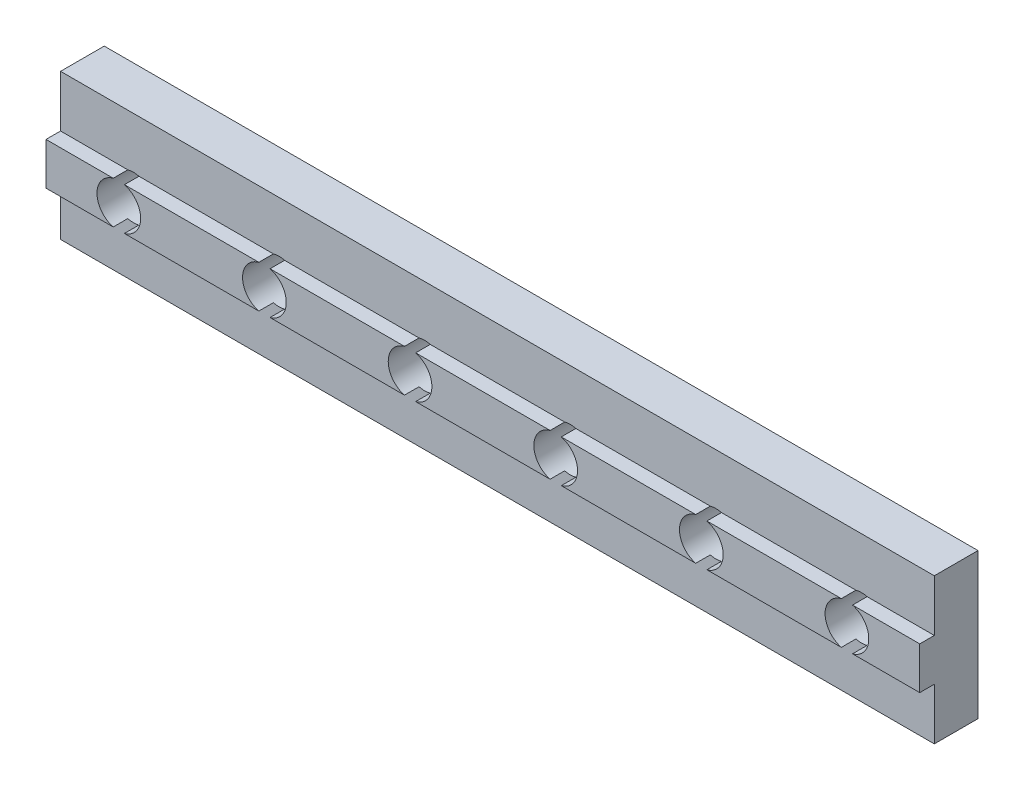
SolidWorks part; units mm, degrees
ref_plane "Front Plane" through (0, 0, 0) normal (0, 0, 1) x (1, 0, 0)
ref_plane "Top Plane" through (0, 0, 0) normal (0, 1, 0) x (1, 0, 0)
ref_plane "Right Plane" through (0, 0, 0) normal (1, 0, 0) x (0, 0, -1)
sketch "Esquisse1" plane through (0, 0, 0) normal (0, 0, 1) x (1, 0, 0)
  line L1 (0, 0) -> (60, 0)
  line L2 (0, 0) -> (0, 10)
  line L3 (0, 10) -> (60, 10)
  line L4 (60, 0) -> (60, 10)
  dimension "D1" = 60
  dimension "D2" = 10
extrude "Boss.-Extru.1" add sketch "Esquisse1" along normal blind 3
sketch "Esquisse2" plane through (0, 0, 3) normal (0, 0, 1) x (1, 0, 0)
  line L0 (60, 0) -> (60, 10) construction
  line L1 (60, 3.55) -> (0, 3.55)
  line L2 (60, 3.55) -> (60, 6.45)
  line L3 (60, 6.45) -> (0, 6.45)
  line L4 (0, 3.55) -> (0, 6.45)
  line L5 (0, 10) -> (0, 0) construction
  point P8 (0, 5)
  point P9 (0, 5)
  dimension "D1" = 2.9
extrude "Boss.-Extru.2" add sketch "Esquisse2" along normal blind 1
sketch "Esquisse3" plane through (0, 0, 0) normal (0, 0, -1) x (-1, 0, 0)
  line L0 (-60, 0) -> (-60, 10) construction
  circle A0 centre (-55, 5) radius 1.5
  point P5 (-60, 5)
  dimension "D1" = 3
  dimension "D2" = 5
extrude "Enlèv. mat.-Extru.1" cut sketch "Esquisse3" against normal through all
pattern_linear "Répétition linéaire1" count 6 spacing 10 along (-1, 0, 0) of "Enlèv. mat.-Extru.1"
